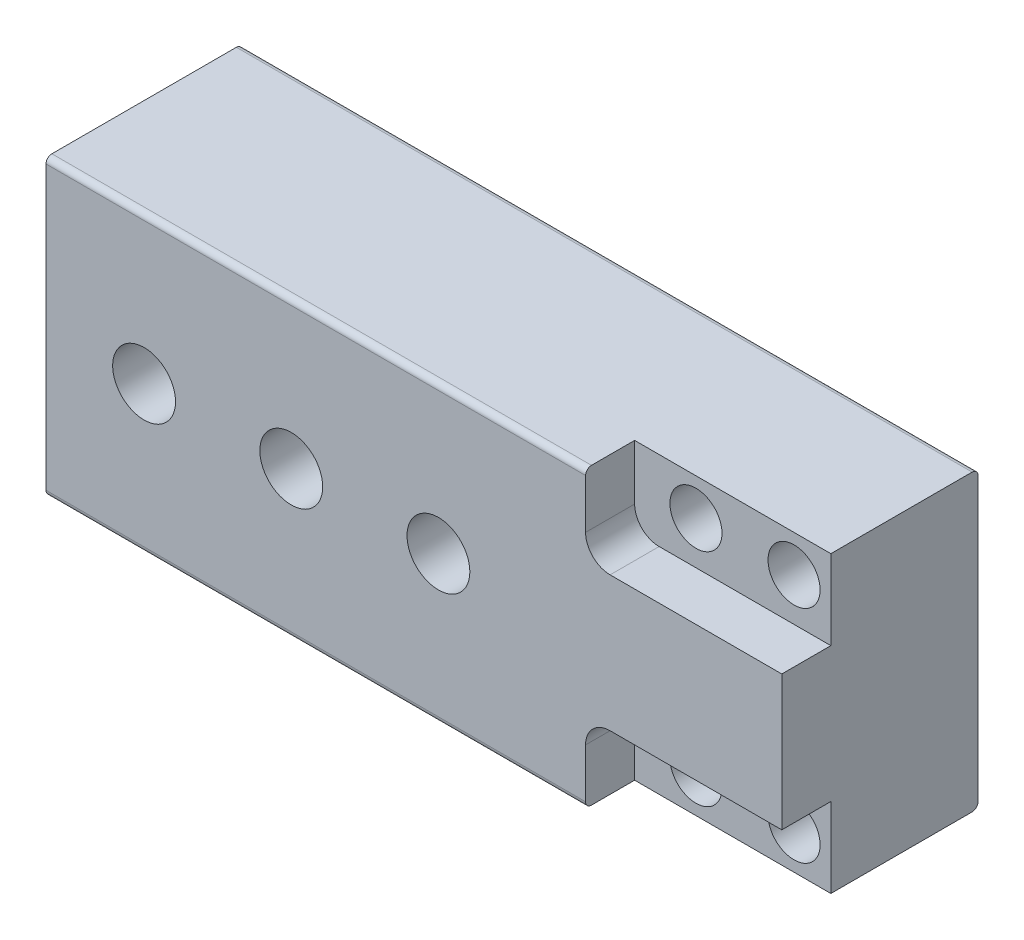
SolidWorks part; units mm, degrees
material "Alloy Steel"
ref_plane "Front" through (0, 0, 0) normal (0, 0, 1) x (1, 0, 0)
ref_plane "Top" through (0, 0, 0) normal (0, 1, 0) x (1, 0, 0)
ref_plane "Right" through (0, 0, 0) normal (1, 0, 0) x (0, 0, -1)
sketch "Sketch1" plane through (0, 0, 0) normal (0, 0, 1) x (1, 0, 0)
  line L0 (0, 0) -> (0, 38.1) construction
  line L1 (-95.25, 38.1) -> (95.25, 38.1)
  line L2 (-95.25, 38.1) -> (-95.25, -38.1)
  line L3 (-95.25, -38.1) -> (95.25, -38.1)
  line L4 (95.25, 38.1) -> (95.25, -38.1)
  line L5 (0, 0) -> (95.25, 0) construction
  dimension "D1" = 76.2
  dimension "D2" = 190.5
extrude "Boss-Extrude1" add sketch "Sketch1" along normal blind 50.8
fillet "Fillet1" radius 1.524 4 edges at (0, 38.1, 0) (0, -38.1, 0) (0, 38.1, 50.8) (0, -38.1, 50.8)
hole_wizard "41/64 (0.64063) Diameter Hole1" positions "Sketch3" profile "Sketch2" hole size "41/64" standard "Ansi Inch"
sketch "Sketch3" plane through (0, 0, 50.8) normal (0, 0, 1) x (1, 0, 0)
  line L1 (-95.25, 0) -> (-69.85, 0) construction
  line L2 (-95.25, 36.576) -> (-95.25, -36.576) construction
  line L3 (-69.85, 0) -> (-31.75, 0) construction
  line L4 (-31.75, 0) -> (6.35, 0) construction
  point P0 (-69.85, 0)
  point P9 (-31.75, 0)
  point P11 (6.35, 0)
  dimension "D1" = 25.4
  dimension "D2" = 38.1
sketch "Sketch2" plane through (-69.85, 0, 50.8) normal (1, 0, 0) x (0, -1, 0)
  line L0 (0, 0) -> (0, 26.162)
  line L1 (0, 26.162) -> (8.136, 26.162)
  line L2 (8.136, 26.162) -> (8.136, 0)
  line L5 (8.136, 0) -> (0, 0)
  line L10 (0, 26.162) -> (-8.136, 26.162) construction
  line L11 (0, -6.35) -> (0, 107.95) construction
  dimension "Hole Dia." = 16.272
  dimension "Hole Depth" = 26.162
  dimension "Drill Angle" = 180
hole_wizard "1/2 (0.5) Diameter Hole1" positions "Sketch5" profile "Sketch6" hole size "1/2" standard "Ansi Inch" end condition through all
sketch "Sketch5" plane through (0, 0, 50.8) normal (0, 0, 1) x (1, 0, 0)
  line L1 (60.325, 28.575) -> (85.725, 28.575) construction
  line L2 (60.325, 28.575) -> (60.325, -28.575) construction
  line L3 (60.325, -28.575) -> (85.725, -28.575) construction
  line L4 (85.725, -28.575) -> (85.725, 28.575) construction
  line L5 (0, 0) -> (85.725, 0) construction
  line L6 (95.25, -36.576) -> (95.25, 36.576) construction
  point P0 (60.325, 28.575)
  point P1 (85.725, 28.575)
  point P5 (60.325, -28.575)
  point P7 (85.725, -28.575)
  dimension "D1" = 57.15
  dimension "D2" = 9.525
  dimension "D3" = 25.4
sketch "Sketch6" plane through (60.325, 28.575, 50.8) normal (1, 0, 0) x (0, -1, 0)
  line L0 (0, 0) -> (0, 50.8)
  line L1 (0, 50.8) -> (6.7437, 50.8)
  line L2 (6.7437, 50.8) -> (6.7437, 0)
  line L5 (6.7437, 0) -> (0, 0)
  line L11 (0, -6.35) -> (0, 107.95) construction
  dimension "Thru Hole Dia." = 13.4874
  dimension "Thru Hole Depth" = 50.8
sketch "Sketch7" plane through (0, 0, 50.8) normal (0, 0, 1) x (1, 0, 0)
  line L0 (-95.25, 38.1) -> (95.25, 38.1) construction
  line L1 (95.25, 38.1) -> (44.45, 38.1)
  line L2 (95.25, 38.1) -> (95.25, 17.4752)
  line L3 (95.25, 17.4752) -> (50.8, 17.4752)
  line L4 (44.45, 38.1) -> (44.45, 23.8252)
  line L6 (95.25, -36.576) -> (95.25, 36.576) construction
  line L7 (95.25, -38.1) -> (-95.25, -38.1) construction
  line L8 (50.8, -17.4752) -> (95.25, -17.4752)
  line L9 (44.45, -23.8252) -> (44.45, -38.1)
  line L10 (44.45, -38.1) -> (95.25, -38.1)
  line L11 (95.25, -17.4752) -> (95.25, -38.1)
  arc A0 (44.45, -23.8252) -> (50.8, -17.4752) centre (50.8, -23.8252) cw
  arc A1 (44.45, 23.8252) -> (50.8, 17.4752) centre (50.8, 23.8252) ccw
  point P18 (44.45, 17.4752)
  dimension "D3" = 6.35
  dimension "D1" = 20.6248
  dimension "D2" = 50.8
extrude "Cut-Extrude1" cut sketch "Sketch7" against normal blind 12.7
